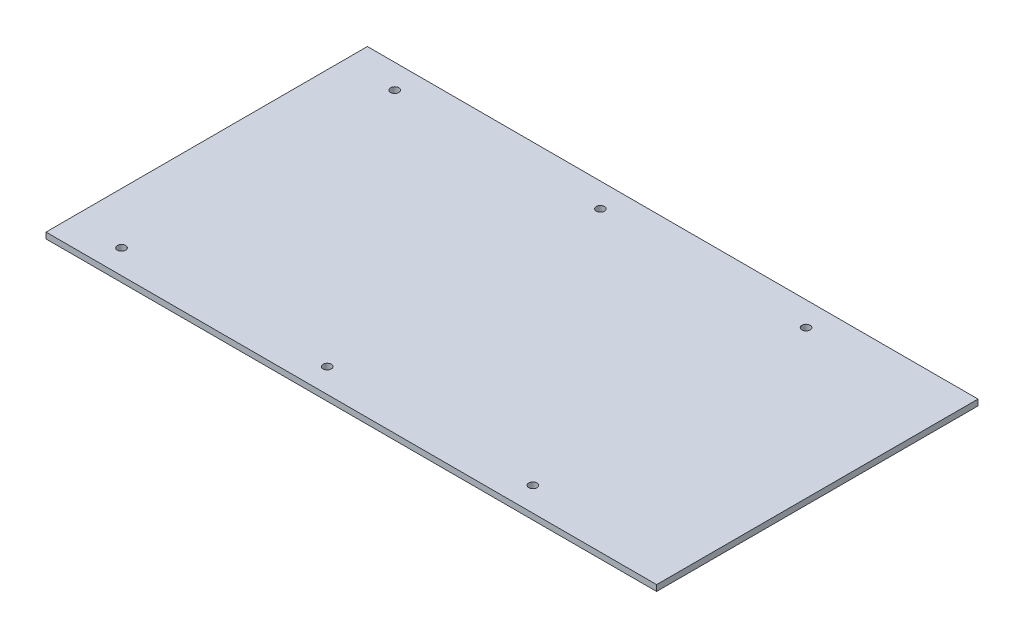
SolidWorks part; units mm, degrees
ref_plane "Front Plane" through (0, 0, 0) normal (0, 0, 1) x (1, 0, 0)
ref_plane "Top Plane" through (0, 0, 0) normal (0, 1, 0) x (1, 0, 0)
ref_plane "Right Plane" through (0, 0, 0) normal (1, 0, 0) x (0, 0, -1)
sketch "Sketch1" plane through (0, 0, 0) normal (0, 1, 0) x (1, 0, 0)
  line L1 (-101.6, 63.5) -> (101.6, 63.5)
  line L2 (-101.6, 63.5) -> (-101.6, -63.5)
  line L3 (-101.6, -63.5) -> (101.6, -63.5)
  line L4 (101.6, 63.5) -> (101.6, -63.5)
  dimension "D1" = 203.2
  dimension "D2" = 127
  dimension "D3" = 63.5
  dimension "D4" = 101.6
extrude "Extrude1" add sketch "Sketch1" along normal blind 2.3622
hole_wizard "#4 Clearance Hole1" positions "3DSketch1" profile "Sketch2" hole size "#4" standard "Ansi Inch"
sketch3d "3DSketch1"
  line L0 (101.6, 2.3622, -63.5) -> (-101.6, 2.3622, -63.5) construction
  line L1 (-101.6, 2.3622, 63.5) -> (101.6, 2.3622, 63.5) construction
  line L2 (-101.6, 2.3622, -63.5) -> (-101.6, 2.3622, 63.5) construction
  line L3 (101.6, 2.3622, 63.5) -> (101.6, 2.3622, -63.5) construction
  line L4 (0, 0, 0) -> (0, 2.3622, -63.5) construction
  point P0 (-81.28, 2.3622, -53.975)
  point P2 (0, 2.3622, -53.975)
  point P4 (0, 2.3622, 53.975)
  point P6 (-81.28, 2.3622, 53.975)
  point P8 (81.28, 2.3622, 53.975)
  point P10 (81.28, 2.3622, -53.975)
  dimension "D1" = 9.525
  dimension "D2" = 9.525
  dimension "D3" = 20.32
  dimension "D4" = 20.32
  dimension "D5" = 101.6
  dimension "D6" = 107.95
sketch "Sketch2" plane through (-81.28, 2.3622, -53.975) normal (1, 0, 0) x (0, 0, 1)
  line L0 (0, 0) -> (0, 7.3306)
  line L1 (0, 7.3306) -> (1.6319, 6.35)
  line L2 (1.6319, 6.35) -> (1.6319, 0)
  line L5 (1.6319, 0) -> (0, 0)
  line L10 (0, 7.3306) -> (-1.632, 6.35) construction
  line L11 (0, -6.35) -> (0, 107.95) construction
  dimension "Hole Dia." = 3.2639
  dimension "Hole Depth" = 6.35
  dimension "Drill Angle" = 118
sketch "Sketch3" plane through (0, 0, 0) normal (0, 1, 0) x (1, 0, 0)
  line L1 (101.6, 63.5) -> (139.7, 63.5)
  line L2 (101.6, 63.5) -> (101.6, -63.5)
  line L3 (101.6, -63.5) -> (139.7, -63.5)
  line L4 (139.7, 63.5) -> (139.7, -63.5)
  dimension "D1" = 38.1
extrude "Extrude2" add sketch "Sketch3" along normal blind 2.3622
